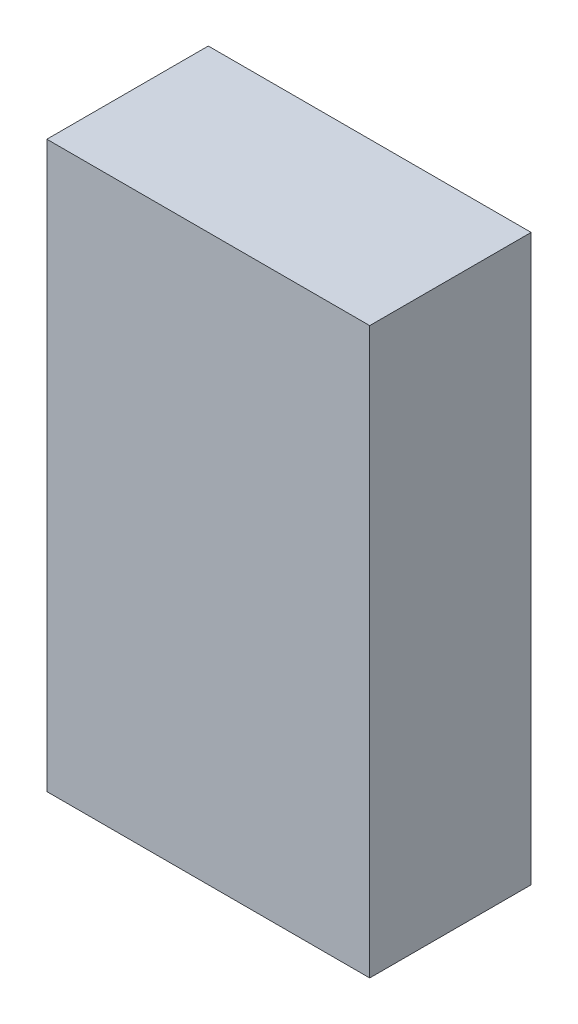
SolidWorks part; units mm, degrees
ref_plane "Front Plane" through (0, 0, 0) normal (0, 0, 1) x (1, 0, 0)
ref_plane "Top Plane" through (0, 0, 0) normal (0, 1, 0) x (1, 0, 0)
ref_plane "Right Plane" through (0, 0, 0) normal (1, 0, 0) x (0, 0, -1)
sketch "Sketch1" plane through (0, 0, 0) normal (0, 0, 1) x (1, 0, 0)
  line L1 (-25.4, -44.45) -> (25.4, -44.45)
  line L2 (-25.4, -44.45) -> (-25.4, 44.45)
  line L3 (-25.4, 44.45) -> (25.4, 44.45)
  line L4 (25.4, -44.45) -> (25.4, 44.45)
  line L5 (-25.4, -44.45) -> (25.4, 44.45) construction
  line L6 (-25.4, 44.45) -> (25.4, -44.45) construction
  point P0 (0, 0)
  dimension "D1" = 50.8
  dimension "D2" = 88.9
extrude "Boss-Extrude1" add sketch "Sketch1" along normal blind 25.4
